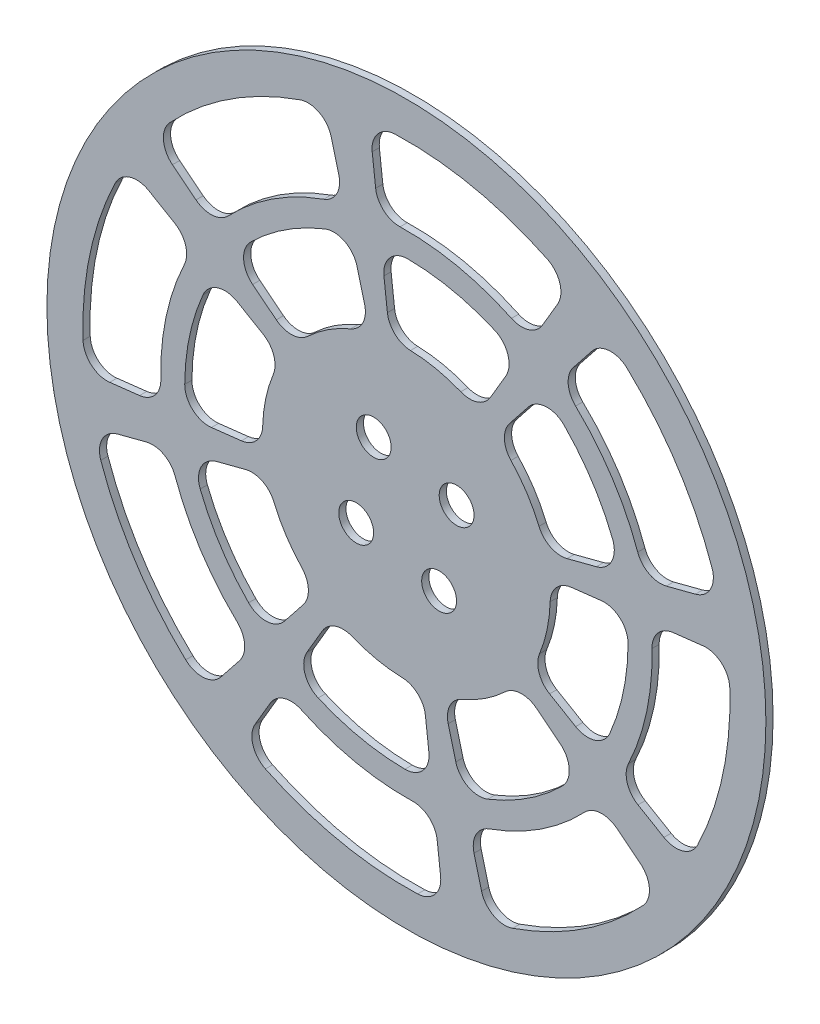
SolidWorks part; units mm, degrees
ref_plane "Front Plane" through (0, 0, 0) normal (0, 0, 1) x (1, 0, 0)
ref_plane "Top Plane" through (0, 0, 0) normal (0, 1, 0) x (1, 0, 0)
ref_plane "Right Plane" through (0, 0, 0) normal (1, 0, 0) x (0, 0, -1)
sketch "Sketch1" plane through (0, 0, 0) normal (0, 0, 1) x (1, 0, 0)
  line L0 (0, 0) -> (0, 140) construction
  line L1 (0, 140) -> (0, 150) construction
  line L2 (-12.5, 140) -> (12.5, 140) construction
  circle A0 centre (0, 0) radius 150
  point P9 (0, 140)
  point P21 (0, 0)
  dimension "D1" = 300
  dimension "D5" = 140
extrude "Boss-Extrude2" add sketch "Sketch1" along normal blind 3
sketch "Sketch2" plane through (0, 0, 0) normal (0, 0, -1) x (-1, 0, 0)
  circle A13 centre (-13.6439, -20.9486) radius 3.2 construction
  circle A14 centre (20.9486, -13.6439) radius 3.2 construction
  circle A15 centre (13.6439, 20.9486) radius 3.2 construction
  circle A16 centre (-20.9486, 13.6439) radius 3.2 construction
  circle A17 centre (-13.6439, -20.9486) radius 3.2
  circle A18 centre (20.9486, -13.6439) radius 3.2
  circle A19 centre (13.6439, 20.9486) radius 3.2
  circle A20 centre (-20.9486, 13.6439) radius 3.2
hole_wizard "CBORE for M6 Hex Head Bolt1" positions "Sketch8" profile "Sketch9" counterbore size "M6" standard "ANSI Metric" end condition through all
sketch "Sketch8" plane through (0, 0, 0) normal (0, 0, -1) x (-1, 0, 0)
  point P0 (-20.9486, 13.6439)
  point P3 (13.6439, 20.9486)
  point P6 (20.9486, -13.6439)
  point P9 (-13.6439, -20.9486)
sketch "Sketch9" plane through (20.9486, 13.6439, 0) normal (1, 0, 0) x (0, 1, 0)
  line L0 (0, 0) -> (0, 3)
  line L1 (0, 3) -> (3.3, 3)
  line L3 (3.3, 3) -> (3.3, 4.38)
  line L4 (3.3, 4.38) -> (7.275, 4.38)
  line L5 (7.275, 4.38) -> (7.275, 0)
  line L7 (7.275, 0) -> (0, 0)
  line L11 (0, -6.35) -> (0, 107.95) construction
  dimension "Thru Hole Dia." = 6.6
  dimension "Thru Hole Depth" = 3
  dimension "C'Bore Dia." = 14.55
  dimension "C'Bore Depth" = 4.38
sketch "Weight Reduction" plane through (0, 0, 0) normal (0, 0, 1) x (1, 0, 0)
  line L0 (-33.9753, 130.6548) -> (0, 0) construction
  line L1 (0, 0) -> (-105.7639, 83.8987) construction
  line L2 (-97.6156, 77.435) -> (-87.7877, 69.6389)
  line L3 (-31.3578, 120.5889) -> (-28.2007, 108.448)
  line L8 (-64.1569, 50.8934) -> (-54.2781, 43.0569)
  line L9 (-20.6096, 79.2559) -> (-17.4361, 67.0521)
  line L38 (0, 0) -> (-15.2146, 81.485) construction
  line L39 (-13.6439, 20.9486) -> (20.9486, 13.6439) construction
  line L40 (20.9486, 13.6439) -> (13.6439, -20.9486) construction
  line L41 (13.6439, -20.9486) -> (-20.9486, -13.6439) construction
  line L42 (-20.9486, -13.6439) -> (-13.6439, 20.9486) construction
  line L43 (-14.2698, 123.7795) -> (-12.8332, 111.3174)
  line L44 (63.096, 107.4425) -> (56.7435, 96.6252)
  line L45 (-9.3787, 81.3529) -> (-7.9346, 68.8262)
  line L46 (41.4692, 70.6155) -> (35.0838, 59.7422)
  line L47 (77.435, 97.6156) -> (69.6389, 87.7877)
  line L48 (120.5889, 31.3578) -> (108.448, 28.2007)
  line L49 (50.8934, 64.1569) -> (43.0569, 54.2781)
  line L50 (79.2559, 20.6096) -> (67.0521, 17.4361)
  line L51 (123.7795, 14.2698) -> (111.3174, 12.8332)
  line L52 (107.4425, -63.096) -> (96.6252, -56.7435)
  line L53 (81.3529, 9.3787) -> (68.8262, 7.9346)
  line L54 (70.6155, -41.4692) -> (59.7422, -35.0838)
  line L55 (97.6156, -77.435) -> (87.7877, -69.6389)
  line L56 (31.3578, -120.5889) -> (28.2007, -108.448)
  line L57 (64.1569, -50.8934) -> (54.2781, -43.0569)
  line L58 (20.6096, -79.2559) -> (17.4361, -67.0521)
  line L59 (14.2698, -123.7795) -> (12.8332, -111.3174)
  line L60 (-63.096, -107.4425) -> (-56.7435, -96.6252)
  line L61 (9.3787, -81.3529) -> (7.9346, -68.8262)
  line L62 (-41.4692, -70.6155) -> (-35.0838, -59.7422)
  line L63 (-77.435, -97.6156) -> (-69.6389, -87.7877)
  line L64 (-120.5889, -31.3578) -> (-108.448, -28.2007)
  line L65 (-50.8934, -64.1569) -> (-43.0569, -54.2781)
  line L66 (-79.2559, -20.6096) -> (-67.0521, -17.4361)
  line L67 (-123.7795, -14.2698) -> (-111.3174, -12.8332)
  line L68 (-107.4425, 63.096) -> (-96.6252, 56.7435)
  line L69 (-81.3529, -9.3787) -> (-68.8262, -7.9346)
  line L70 (-70.6155, 41.4692) -> (-59.7422, 35.0838)
  arc A0 (-98.713, 92.091) -> (-44.3188, 127.518) centre (0, 0) cw
  arc A1 (-74.322, 70.5867) -> (-34.5118, 96.5152) centre (0, 0) cw
  arc A2 (-64.9655, 65.8463) -> (-33.9589, 86.0409) centre (0, 0) cw
  arc A3 (-41.1971, 43.621) -> (-23.2408, 55.3161) centre (0, 0) cw
  arc A4 (-23.2408, 55.3161) -> (-17.4361, 67.0521) centre (-27.1143, 64.5354) ccw
  arc A5 (-41.1971, 43.621) -> (-54.2781, 43.0569) centre (-48.0633, 50.8912) cw
  arc A6 (-33.9589, 86.0409) -> (-20.6096, 79.2559) centre (-30.2877, 76.7392) cw
  arc A7 (-64.9655, 65.8463) -> (-64.1569, 50.8934) centre (-57.9422, 58.7278) ccw
  arc A8 (-34.5118, 96.5152) -> (-28.2007, 108.448) centre (-37.8788, 105.9313) ccw
  arc A9 (-74.322, 70.5867) -> (-87.7877, 69.6389) centre (-81.573, 77.4732) cw
  arc A10 (-44.3188, 127.518) -> (-31.3578, 120.5889) centre (-41.0359, 118.0722) cw
  arc A11 (-98.713, 92.091) -> (-97.6156, 77.435) centre (-91.4009, 85.2694) ccw
  arc A12 (-2.6413, 102.466) -> (-12.8332, 111.3174) centre (-2.899, 112.4626) cw
  arc A13 (-2.6413, 102.466) -> (43.843, 92.6501) centre (0, 0) cw
  arc A14 (43.843, 92.6501) -> (56.7435, 96.6252) centre (48.1204, 101.6891) ccw
  arc A15 (58.8308, 121.507) -> (63.096, 107.4425) centre (54.4729, 112.5064) cw
  arc A16 (-4.6825, 134.9188) -> (58.8308, 121.507) centre (0, 0) cw
  arc A17 (-4.6825, 134.9188) -> (-14.2698, 123.7795) centre (-4.3356, 124.9248) ccw
  arc A18 (1.714, 59.9755) -> (-7.9346, 68.8262) centre (1.9996, 69.9714) cw
  arc A19 (1.714, 59.9755) -> (22.6806, 55.5481) centre (0, 0) cw
  arc A20 (22.6806, 55.5481) -> (35.0838, 59.7422) centre (26.4607, 64.8061) ccw
  arc A21 (36.8275, 84.8527) -> (41.4692, 70.6155) centre (32.8462, 75.6795) cw
  arc A22 (0.6228, 92.4979) -> (36.8275, 84.8527) centre (0, 0) cw
  arc A23 (0.6228, 92.4979) -> (-9.3787, 81.3529) centre (0.5555, 82.4981) ccw
  arc A24 (70.5867, 74.322) -> (69.6389, 87.7877) centre (77.4732, 81.573) cw
  arc A25 (70.5867, 74.322) -> (96.5152, 34.5118) centre (0, 0) cw
  arc A26 (96.5152, 34.5118) -> (108.448, 28.2007) centre (105.9313, 37.8788) ccw
  arc A27 (127.518, 44.3188) -> (120.5889, 31.3578) centre (118.0722, 41.0359) cw
  arc A28 (92.091, 98.713) -> (127.518, 44.3188) centre (0, 0) cw
  arc A29 (92.091, 98.713) -> (77.435, 97.6156) centre (85.2694, 91.4009) ccw
  arc A30 (43.621, 41.1971) -> (43.0569, 54.2781) centre (50.8912, 48.0633) cw
  arc A31 (43.621, 41.1971) -> (55.3161, 23.2408) centre (0, 0) cw
  arc A32 (55.3161, 23.2408) -> (67.0521, 17.4361) centre (64.5354, 27.1143) ccw
  arc A33 (86.0409, 33.9589) -> (79.2559, 20.6096) centre (76.7392, 30.2877) cw
  arc A34 (65.8463, 64.9655) -> (86.0409, 33.9589) centre (0, 0) cw
  arc A35 (65.8463, 64.9655) -> (50.8934, 64.1569) centre (58.7278, 57.9422) ccw
  arc A36 (102.466, 2.6413) -> (111.3174, 12.8332) centre (112.4626, 2.899) cw
  arc A37 (102.466, 2.6413) -> (92.6501, -43.843) centre (0, 0) cw
  arc A38 (92.6501, -43.843) -> (96.6252, -56.7435) centre (101.6891, -48.1204) ccw
  arc A39 (121.507, -58.8308) -> (107.4425, -63.096) centre (112.5064, -54.4729) cw
  arc A40 (134.9188, 4.6825) -> (121.507, -58.8308) centre (0, 0) cw
  arc A41 (134.9188, 4.6825) -> (123.7795, 14.2698) centre (124.9248, 4.3356) ccw
  arc A42 (59.9755, -1.714) -> (68.8262, 7.9346) centre (69.9714, -1.9996) cw
  arc A43 (59.9755, -1.714) -> (55.5481, -22.6806) centre (0, 0) cw
  arc A44 (55.5481, -22.6806) -> (59.7422, -35.0838) centre (64.8061, -26.4607) ccw
  arc A45 (84.8527, -36.8275) -> (70.6155, -41.4692) centre (75.6795, -32.8462) cw
  arc A46 (92.4979, -0.6228) -> (84.8527, -36.8275) centre (0, 0) cw
  arc A47 (92.4979, -0.6228) -> (81.3529, 9.3787) centre (82.4981, -0.5555) ccw
  arc A48 (74.322, -70.5867) -> (87.7877, -69.6389) centre (81.573, -77.4732) cw
  arc A49 (74.322, -70.5867) -> (34.5118, -96.5152) centre (0, 0) cw
  arc A50 (34.5118, -96.5152) -> (28.2007, -108.448) centre (37.8788, -105.9313) ccw
  arc A51 (44.3188, -127.518) -> (31.3578, -120.5889) centre (41.0359, -118.0722) cw
  arc A52 (98.713, -92.091) -> (44.3188, -127.518) centre (0, 0) cw
  arc A53 (98.713, -92.091) -> (97.6156, -77.435) centre (91.4009, -85.2694) ccw
  arc A54 (41.1971, -43.621) -> (54.2781, -43.0569) centre (48.0633, -50.8912) cw
  arc A55 (41.1971, -43.621) -> (23.2408, -55.3161) centre (0, 0) cw
  arc A56 (23.2408, -55.3161) -> (17.4361, -67.0521) centre (27.1143, -64.5354) ccw
  arc A57 (33.9589, -86.0409) -> (20.6096, -79.2559) centre (30.2877, -76.7392) cw
  arc A58 (64.9655, -65.8463) -> (33.9589, -86.0409) centre (0, 0) cw
  arc A59 (64.9655, -65.8463) -> (64.1569, -50.8934) centre (57.9422, -58.7278) ccw
  arc A60 (2.6413, -102.466) -> (12.8332, -111.3174) centre (2.899, -112.4626) cw
  arc A61 (2.6413, -102.466) -> (-43.843, -92.6501) centre (0, 0) cw
  arc A62 (-43.843, -92.6501) -> (-56.7435, -96.6252) centre (-48.1204, -101.6891) ccw
  arc A63 (-58.8308, -121.507) -> (-63.096, -107.4425) centre (-54.4729, -112.5064) cw
  arc A64 (4.6825, -134.9188) -> (-58.8308, -121.507) centre (0, 0) cw
  arc A65 (4.6825, -134.9188) -> (14.2698, -123.7795) centre (4.3356, -124.9248) ccw
  arc A66 (-1.714, -59.9755) -> (7.9346, -68.8262) centre (-1.9996, -69.9714) cw
  arc A67 (-1.714, -59.9755) -> (-22.6806, -55.5481) centre (0, 0) cw
  arc A68 (-22.6806, -55.5481) -> (-35.0838, -59.7422) centre (-26.4607, -64.8061) ccw
  arc A69 (-36.8275, -84.8527) -> (-41.4692, -70.6155) centre (-32.8462, -75.6795) cw
  arc A70 (-0.6228, -92.4979) -> (-36.8275, -84.8527) centre (0, 0) cw
  arc A71 (-0.6228, -92.4979) -> (9.3787, -81.3529) centre (-0.5555, -82.4981) ccw
  arc A72 (-70.5867, -74.322) -> (-69.6389, -87.7877) centre (-77.4732, -81.573) cw
  arc A73 (-70.5867, -74.322) -> (-96.5152, -34.5118) centre (0, 0) cw
  arc A74 (-96.5152, -34.5118) -> (-108.448, -28.2007) centre (-105.9313, -37.8788) ccw
  arc A75 (-127.518, -44.3188) -> (-120.5889, -31.3578) centre (-118.0722, -41.0359) cw
  arc A76 (-92.091, -98.713) -> (-127.518, -44.3188) centre (0, 0) cw
  arc A77 (-92.091, -98.713) -> (-77.435, -97.6156) centre (-85.2694, -91.4009) ccw
  arc A78 (-43.621, -41.1971) -> (-43.0569, -54.2781) centre (-50.8912, -48.0633) cw
  arc A79 (-43.621, -41.1971) -> (-55.3161, -23.2408) centre (0, 0) cw
  arc A80 (-55.3161, -23.2408) -> (-67.0521, -17.4361) centre (-64.5354, -27.1143) ccw
  arc A81 (-86.0409, -33.9589) -> (-79.2559, -20.6096) centre (-76.7392, -30.2877) cw
  arc A82 (-65.8463, -64.9655) -> (-86.0409, -33.9589) centre (0, 0) cw
  arc A83 (-65.8463, -64.9655) -> (-50.8934, -64.1569) centre (-58.7278, -57.9422) ccw
  arc A84 (-102.466, -2.6413) -> (-111.3174, -12.8332) centre (-112.4626, -2.899) cw
  arc A85 (-102.466, -2.6413) -> (-92.6501, 43.843) centre (0, 0) cw
  arc A86 (-92.6501, 43.843) -> (-96.6252, 56.7435) centre (-101.6891, 48.1204) ccw
  arc A87 (-121.507, 58.8308) -> (-107.4425, 63.096) centre (-112.5064, 54.4729) cw
  arc A88 (-134.9188, -4.6825) -> (-121.507, 58.8308) centre (0, 0) cw
  arc A89 (-134.9188, -4.6825) -> (-123.7795, -14.2698) centre (-124.9248, -4.3356) ccw
  arc A90 (-59.9755, 1.714) -> (-68.8262, -7.9346) centre (-69.9714, 1.9996) cw
  arc A91 (-59.9755, 1.714) -> (-55.5481, 22.6806) centre (0, 0) cw
  arc A92 (-55.5481, 22.6806) -> (-59.7422, 35.0838) centre (-64.8061, 26.4607) ccw
  arc A93 (-84.8527, 36.8275) -> (-70.6155, 41.4692) centre (-75.6795, 32.8462) cw
  arc A94 (-92.4979, 0.6228) -> (-84.8527, 36.8275) centre (0, 0) cw
  arc A95 (-92.4979, 0.6228) -> (-81.3529, -9.3787) centre (-82.4981, 0.5555) ccw
  point P198 (0, 0)
  point P200 (0, 0)
  dimension "D3" = 60
  dimension "D4" = 92.5
  dimension "D5" = 102.5
  dimension "D6" = 135
  dimension "D7" = 10
  dimension "D1" = 4
  dimension "D2" = 37
  dimension "D8" = 22.5
  dimension "D9" = 8
extrude "Cutouts" cut sketch "Weight Reduction" along normal through all
equation "\"D1@Weight Reduction\"=(45-\"D2@Weight Reduction\")/2"
